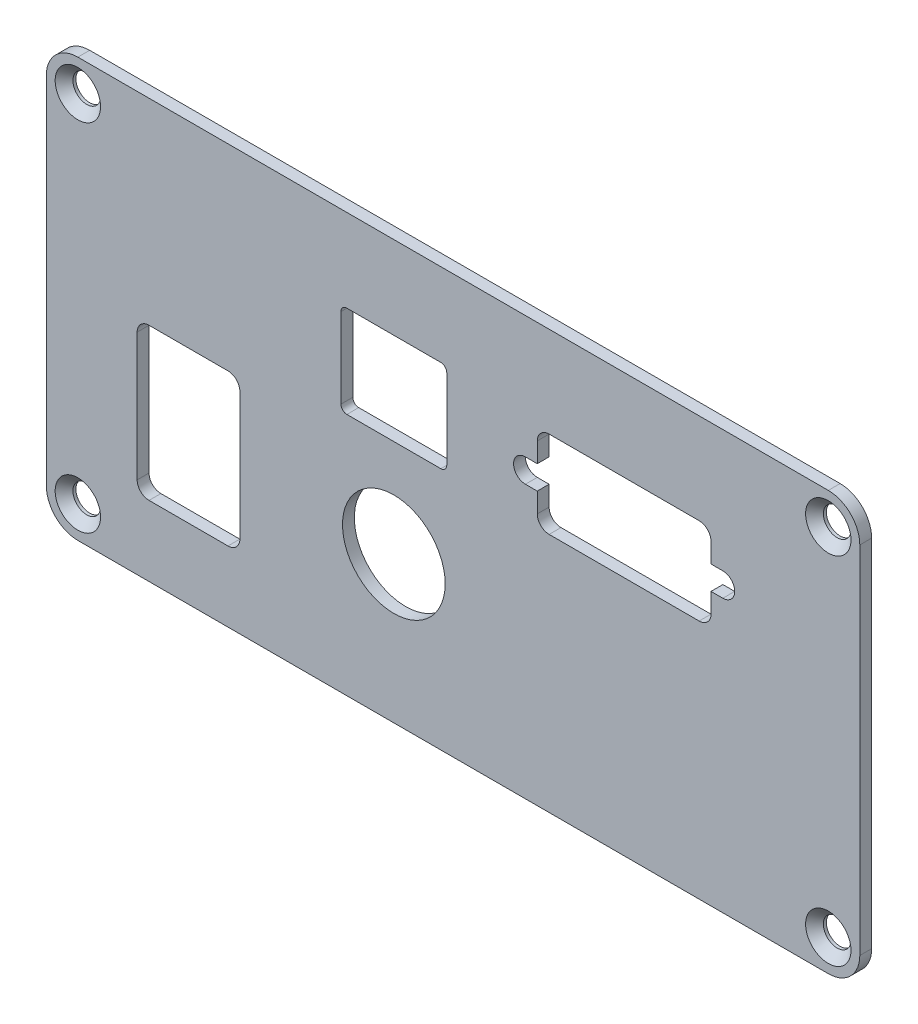
SolidWorks part; units mm, degrees
ref_plane "Plan de face" through (0, 0, 0) normal (0, 0, 1) x (1, 0, 0)
ref_plane "Plan de dessus" through (0, 0, 0) normal (0, 1, 0) x (1, 0, 0)
ref_plane "Plan de droite" through (0, 0, 0) normal (1, 0, 0) x (0, 0, -1)
ref_plane "Plan1" through (0, 0, -0.75) normal (0, 0, -1) x (-1, 0, 0)
sketch "Esquisse1" plane through (0, 0, -0.75) normal (0, 0, -1) x (-1, 0, 0)
  line L0 (-51.5, -26.5) -> (51.5, -26.5)
  line L1 (51.5, -26.5) -> (51.5, 26.5)
  line L2 (51.5, 26.5) -> (-51.5, 26.5)
  line L3 (-51.5, 26.5) -> (-51.5, -26.5)
extrude "Boss.-Extru.1" add sketch "Esquisse1" against normal blind 1.5
hole_wizard "Fraisage pour vis à tête fraisée M31" positions "Esquisse3" profile "Esquisse2" countersink size "M3" standard "Ansi Metric"
sketch "Esquisse3" plane through (0, 0, 0.75) normal (0, 0, 1) x (1, 0, 0)
  point P0 (-47.51, 22.5)
  point P1 (47.51, 22.5)
  point P2 (47.51, -22.5)
  point P3 (-47.51, -22.5)
sketch "Esquisse2" plane through (-47.51, 22.5, 0.75) normal (1, 0, 0) x (0, -1, 0)
  line L0 (0, 0) -> (0, 1.5)
  line L1 (0, 1.5) -> (1.75, 1.5)
  line L2 (1.75, 1.5) -> (1.75, 1.125)
  line L3 (1.75, 1.125) -> (2.875, 0)
  line L5 (2.875, 0) -> (0, 0)
  line L6 (-1.75, 1.125) -> (-2.875, 0) construction
  line L11 (0, -6.35) -> (0, 107.95) construction
  dimension "Diamètre du perçage jusqu'au prochain" = 3.5
  dimension "Profondeur du perçage jusqu'au prochain" = 1.5
  dimension "Diamètre du fraisage entrant" = 5.75
  dimension "Angle du fraisage entrant" = 90
fillet "Congé1" radius 3.99 4 edges at (51.5, 26.5, 0) (51.5, -26.5, 0) (-51.5, 26.5, 0) (-51.5, -26.5, 0)
sketch "Esquisse5" plane through (0, 0, 0.75) normal (0, 0, 1) x (1, 0, 0)
  line L0 (-51.5, 0) -> (51.5, 0) construction
  line L1 (-51.5, -22.51) -> (-51.5, 22.51) construction
  line L2 (51.5, 22.51) -> (51.5, -22.51) construction
  line L3 (0, 26.5) -> (0, -26.5) construction
  line L4 (-47.51, 26.5) -> (47.51, 26.5) construction
  line L5 (47.51, -26.5) -> (-47.51, -26.5) construction
  line L6 (21.66, 15) -> (21.66, 4) construction
  line L7 (-28.5, -17.6) -> (-38.5, -17.6)
  line L8 (-27, -16.1) -> (-27, 0.1)
  line L9 (-28.5, 1.6) -> (-38.5, 1.6)
  line L10 (-40, -16.1) -> (-40, 0.1)
  line L11 (-27, -17.6) -> (-40, 1.6) construction
  line L12 (-27, 1.6) -> (-40, -17.6) construction
  line L13 (31.16, 4) -> (12.16, 4)
  line L14 (32.66, 5.5) -> (32.66, 8)
  line L15 (31.16, 15) -> (12.16, 15)
  line L16 (10.66, 5.5) -> (10.66, 8)
  line L17 (32.66, 4) -> (10.66, 15) construction
  line L18 (32.66, 15) -> (10.66, 4) construction
  line L19 (34.16, 11) -> (32.66, 11)
  line L20 (34.16, 8) -> (32.66, 8)
  line L21 (32.66, 11) -> (32.66, 13.5)
  line L22 (9.16, 8) -> (10.66, 8)
  line L23 (9.16, 11) -> (10.66, 11)
  line L24 (10.66, 11) -> (10.66, 13.5)
  line L25 (34.16, 9.5) -> (9.16, 9.5) construction
  line L26 (-13.45, 4.35) -> (-1.55, 4.35)
  line L27 (-14.2, 5.1) -> (-14.2, 15.25)
  line L28 (-13.45, 16) -> (-1.55, 16)
  line L29 (-0.8, 5.1) -> (-0.8, 15.25)
  line L30 (-14.2, 4.35) -> (-0.8, 16) construction
  line L31 (-14.2, 16) -> (-0.8, 4.35) construction
  arc A0 (34.16, 8) -> (34.16, 11) centre (34.16, 9.5) ccw
  arc A1 (9.16, 8) -> (9.16, 11) centre (9.16, 9.5) cw
  circle A2 centre (-7.5, -8) radius 6.5
  arc A3 (-27, 0.1) -> (-28.5, 1.6) centre (-28.5, 0.1) ccw
  arc A4 (-38.5, 1.6) -> (-40, 0.1) centre (-38.5, 0.1) ccw
  arc A5 (-40, -16.1) -> (-38.5, -17.6) centre (-38.5, -16.1) ccw
  arc A6 (-28.5, -17.6) -> (-27, -16.1) centre (-28.5, -16.1) ccw
  arc A7 (32.66, 5.5) -> (31.16, 4) centre (31.16, 5.5) cw
  arc A8 (12.16, 4) -> (10.66, 5.5) centre (12.16, 5.5) cw
  arc A9 (10.66, 13.5) -> (12.16, 15) centre (12.16, 13.5) cw
  arc A10 (32.66, 13.5) -> (31.16, 15) centre (31.16, 13.5) ccw
  arc A11 (-14.2, 15.25) -> (-13.45, 16) centre (-13.45, 15.25) cw
  arc A12 (-0.8, 5.1) -> (-1.55, 4.35) centre (-1.55, 5.1) cw
  arc A13 (-0.8, 15.25) -> (-1.55, 16) centre (-1.55, 15.25) ccw
  arc A14 (-14.2, 5.1) -> (-13.45, 4.35) centre (-13.45, 5.1) ccw
  point P12 (-33.5, -8)
  point P17 (21.66, 9.5)
  point P60 (-7.5, 10.175)
  dimension "D9" = 25
  dimension "D10" = 1.5
  dimension "D11" = 13
  dimension "D14" = 1.5
  dimension "D19" = 0.75
  dimension "D2" = 8
  dimension "D3" = 19.2
  dimension "D4" = 13
  dimension "D6" = 22
  dimension "D7" = 11
  dimension "D8" = 17
  dimension "D12" = 26
  dimension "D13" = 18
  dimension "D15" = 13.4
  dimension "D16" = 11.65
  dimension "D17" = 29.16
  dimension "D18" = 6.5
extrude "Enlèv. mat.-Extru.1" cut sketch "Esquisse5" against normal through all
